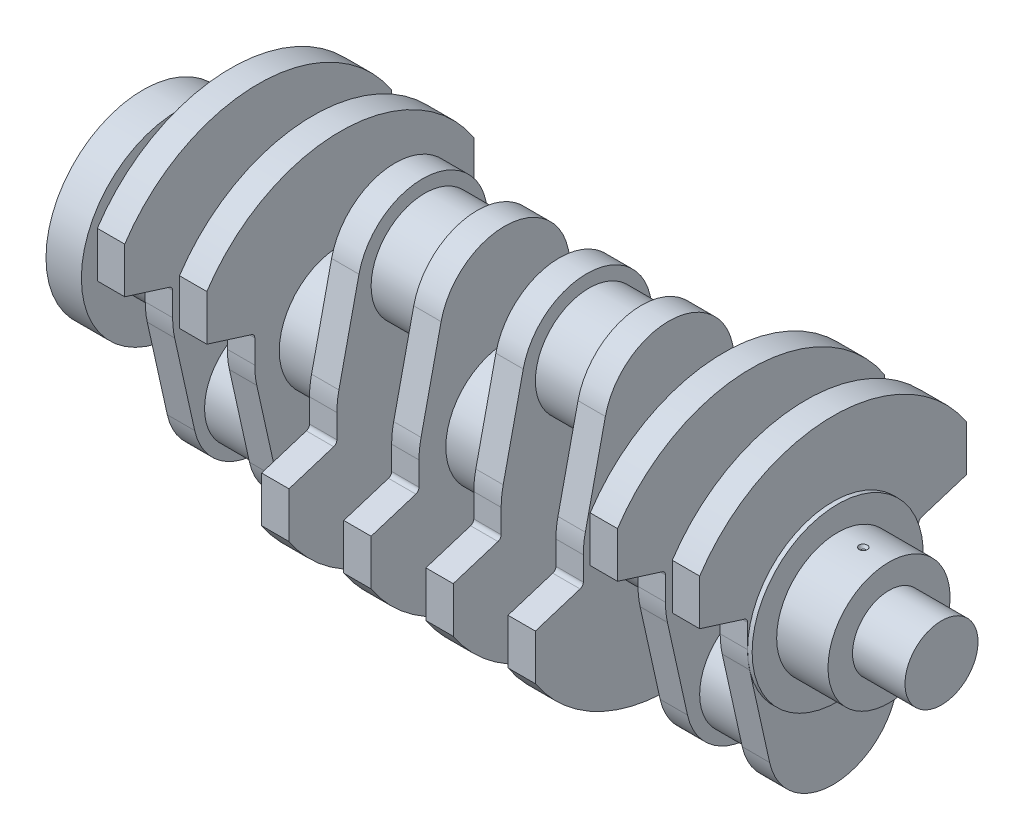
SolidWorks part; units mm, degrees
ref_plane "Plano frontal" through (0, 0, 0) normal (0, 0, 1) x (1, 0, 0)
ref_plane "Plano superior" through (0, 0, 0) normal (0, 1, 0) x (1, 0, 0)
ref_plane "Plano direito" through (0, 0, 0) normal (1, 0, 0) x (0, 0, -1)
sketch "Esboço1" plane through (0, 0, 0) normal (1, 0, 0) x (0, 0, -1)
  circle A0 centre (0, 0) radius 16
  dimension "D1" = 32
extrude "Extrusão1" add sketch "Esboço1" against normal blind 23
sketch "Esboço2" plane through (-23, 0, 0) normal (-1, 0, 0) x (0, 0, 1)
  circle A0 centre (0, 0) radius 26.75
  dimension "D1" = 53.5
extrude "Extrusão2" add sketch "Esboço2" along normal blind 22.5
ref_plane "Plano1" through (-47.5, 0, 0) normal (-1, 0, 0) x (0, 0, 1)
sketch "Esboço5" plane through (-47.5, 0, 0) normal (-1, 0, 0) x (0, 0, 1)
  line L1 (-36.6075, -8.1325) -> (-27.8217, -47.6807)
  line L2 (36.6075, -8.1325) -> (27.8217, -47.6807)
  line L3 (0, 67.381) -> (0, 70) construction
  line L5 (-58.5, 38.4415) -> (-58.5, 18.4415)
  line L6 (58.5, 38.4415) -> (58.5, 18.4415)
  line L7 (-58.5, 18.4415) -> (-37.5, 11.8215)
  line L8 (58.5, 18.4415) -> (37.5, 11.8215)
  line L9 (-37.5, 11.8215) -> (-37.5, 0)
  line L10 (37.5, 11.8215) -> (37.5, 0)
  arc A0 (36.6075, -8.1325) -> (37.5, 0) centre (0, 0) ccw
  arc A1 (-27.8217, -47.6807) -> (27.8217, -47.6807) centre (0, -41.5) ccw
  arc A2 (-58.5, 38.4415) -> (58.5, 38.4415) centre (0, 0) cw
  arc A3 (-37.5, 0) -> (-36.6075, -8.1325) centre (0, 0) ccw
  dimension "D1" = 75
  dimension "D3" = 57
  dimension "D4" = 70
  dimension "D2" = 41.5
  dimension "D5" = 20
  dimension "D6" = 20
extrude "Extrusão4" add sketch "Esboço5" along normal blind 12 separate body
fillet "Filete1" radius 2 1 edges at (-53.5, 11.8215, -37.5)
fillet "Filete2" radius 2 1 edges at (-53.5, 11.8215, 37.5)
ref_plane "Plano2" through (-83.5, 0, 0) normal (-1, 0, 0) x (0, 0, 1)
sketch "Esboço9" plane through (-83.5, 0, 0) normal (-1, 0, 0) x (0, 0, 1)
  line L24 (27.8217, -47.6807) -> (36.6075, -8.1325)
  line L25 (37.5, 0) -> (37.5, 10.3549)
  line L26 (38.8987, 12.2624) -> (58.5, 18.4415)
  line L27 (58.5, 18.4415) -> (58.5, 38.4415)
  line L28 (-58.5, 38.4415) -> (-58.5, 18.4415)
  line L29 (-58.5, 18.4415) -> (-38.8987, 12.2624)
  line L30 (-37.5, 10.3549) -> (-37.5, 0)
  line L31 (-36.6075, -8.1325) -> (-27.8217, -47.6807)
  line L32 (27.8217, -47.6807) -> (36.6075, -8.1325)
  line L33 (37.5, 0) -> (37.5, 10.3549)
  line L34 (38.8987, 12.2624) -> (58.5, 18.4415)
  line L35 (58.5, 18.4415) -> (58.5, 38.4415)
  line L36 (-58.5, 38.4415) -> (-58.5, 18.4415)
  line L37 (-58.5, 18.4415) -> (-38.8987, 12.2624)
  line L38 (-37.5, 10.3549) -> (-37.5, 0)
  line L39 (-36.6075, -8.1325) -> (-27.8217, -47.6807)
  arc A18 (-27.8217, -47.6807) -> (27.8217, -47.6807) centre (0, -41.5) ccw
  arc A19 (36.6075, -8.1325) -> (37.5, 0) centre (0, 0) ccw
  arc A20 (38.8987, 12.2624) -> (37.5, 10.3549) centre (39.5, 10.3549) ccw
  arc A21 (58.5, 38.4415) -> (-58.5, 38.4415) centre (0, 0) ccw
  arc A22 (-37.5, 10.3549) -> (-38.8987, 12.2624) centre (-39.5, 10.3549) ccw
  arc A23 (-37.5, 0) -> (-36.6075, -8.1325) centre (0, 0) ccw
  arc A24 (-27.8217, -47.6807) -> (27.8217, -47.6807) centre (0, -41.5) ccw
  arc A25 (36.6075, -8.1325) -> (37.5, 0) centre (0, 0) ccw
  arc A26 (38.8987, 12.2624) -> (37.5, 10.3549) centre (39.5, 10.3549) ccw
  arc A27 (58.5, 38.4415) -> (-58.5, 38.4415) centre (0, 0) ccw
  arc A28 (-37.5, 10.3549) -> (-38.8987, 12.2624) centre (-39.5, 10.3549) ccw
  arc A29 (-37.5, 0) -> (-36.6075, -8.1325) centre (0, 0) ccw
  dimension "D1" = 0
sketch "Esboço10" plane through (-59.5, 0, 0) normal (-1, 0, 0) x (0, 0, 1)
  circle A0 centre (0, -41.5) radius 23.5
  dimension "D1" = 47
extrude "Extrusão7" add sketch "Esboço10" along normal blind 23
extrude "Extrusão8" add sketch "Esboço9" along normal blind 12
ref_plane "Plano5" through (-119.5, 0, 0) normal (-1, 0, 0) x (0, 0, 1)
sketch "Esboço16" plane through (-119.5, 0, 0) normal (-1, 0, 0) x (0, 0, 1)
  line L17 (37.5, 0) -> (37.5, -10.3549)
  line L18 (38.8987, -12.2624) -> (58.5, -18.4415)
  line L19 (-58.5, -38.4415) -> (-58.5, -18.4415)
  line L20 (-58.5, -18.4415) -> (-38.8987, -12.2624)
  line L21 (-37.5, -10.3549) -> (-37.5, 0)
  line L22 (58.5, -18.4415) -> (58.5, -38.4415)
  line L23 (27.8217, 47.6807) -> (36.6075, 8.1325)
  line L24 (-36.6075, 8.1325) -> (-27.8217, 47.6807)
  arc A12 (-37.5, -10.3549) -> (-38.8987, -12.2624) centre (-39.5, -10.3549) cw
  arc A13 (38.8987, -12.2624) -> (37.5, -10.3549) centre (39.5, -10.3549) cw
  arc A14 (-37.5, 0) -> (-36.6075, 8.1325) centre (0, 0) cw
  arc A15 (36.6075, 8.1325) -> (37.5, 0) centre (0, 0) cw
  arc A16 (58.5, -38.4415) -> (-58.5, -38.4415) centre (0, 0) cw
  arc A17 (-27.8217, 47.6807) -> (27.8217, 47.6807) centre (0, 41.5) cw
extrude "Extrusão14" add sketch "Esboço16" along normal blind 12 separate body
ref_plane "Plano6" through (-155.5, 0, 0) normal (-1, 0, 0) x (0, 0, 1)
sketch "Esboço17" plane through (-155.5, 0, 0) normal (-1, 0, 0) x (0, 0, 1)
  line L16 (-38.8987, -12.2624) -> (-58.5, -18.4415)
  line L17 (-58.5, -18.4415) -> (-58.5, -38.4415)
  line L18 (58.5, -38.4415) -> (58.5, -18.4415)
  line L19 (58.5, -18.4415) -> (38.8987, -12.2624)
  line L20 (37.5, -10.3549) -> (37.5, 0)
  line L21 (36.6075, 8.1325) -> (27.8217, 47.6807)
  line L22 (-27.8217, 47.6807) -> (-36.6075, 8.1325)
  line L23 (-37.5, 0) -> (-37.5, -10.3549)
  line L24 (-38.8987, -12.2624) -> (-58.5, -18.4415)
  line L25 (-58.5, -18.4415) -> (-58.5, -38.4415)
  line L26 (58.5, -38.4415) -> (58.5, -18.4415)
  line L27 (58.5, -18.4415) -> (38.8987, -12.2624)
  line L28 (37.5, -10.3549) -> (37.5, 0)
  line L29 (36.6075, 8.1325) -> (27.8217, 47.6807)
  line L30 (-27.8217, 47.6807) -> (-36.6075, 8.1325)
  line L31 (-37.5, 0) -> (-37.5, -10.3549)
  arc A12 (-38.8987, -12.2624) -> (-37.5, -10.3549) centre (-39.5, -10.3549) ccw
  arc A13 (-58.5, -38.4415) -> (58.5, -38.4415) centre (0, 0) ccw
  arc A14 (37.5, -10.3549) -> (38.8987, -12.2624) centre (39.5, -10.3549) ccw
  arc A15 (37.5, 0) -> (36.6075, 8.1325) centre (0, 0) ccw
  arc A16 (27.8217, 47.6807) -> (-27.8217, 47.6807) centre (0, 41.5) ccw
  arc A17 (-36.6075, 8.1325) -> (-37.5, 0) centre (0, 0) ccw
  arc A18 (-38.8987, -12.2624) -> (-37.5, -10.3549) centre (-39.5, -10.3549) ccw
  arc A19 (-58.5, -38.4415) -> (58.5, -38.4415) centre (0, 0) ccw
  arc A20 (37.5, -10.3549) -> (38.8987, -12.2624) centre (39.5, -10.3549) ccw
  arc A21 (37.5, 0) -> (36.6075, 8.1325) centre (0, 0) ccw
  arc A22 (27.8217, 47.6807) -> (-27.8217, 47.6807) centre (0, 41.5) ccw
  arc A23 (-36.6075, 8.1325) -> (-37.5, 0) centre (0, 0) ccw
  dimension "D1" = 0
extrude "Extrusão15" add sketch "Esboço17" along normal blind 12 separate body
ref_plane "Plano7" through (-191.5, 0, 0) normal (-1, 0, 0) x (0, 0, 1)
sketch "Esboço18" plane through (-191.5, 0, 0) normal (-1, 0, 0) x (0, 0, 1)
  line L16 (-38.8987, -12.2624) -> (-58.5, -18.4415)
  line L17 (-58.5, -18.4415) -> (-58.5, -38.4415)
  line L18 (58.5, -38.4415) -> (58.5, -18.4415)
  line L19 (58.5, -18.4415) -> (38.8987, -12.2624)
  line L20 (37.5, -10.3549) -> (37.5, 0)
  line L21 (36.6075, 8.1325) -> (27.8217, 47.6807)
  line L22 (-27.8217, 47.6807) -> (-36.6075, 8.1325)
  line L23 (-37.5, 0) -> (-37.5, -10.3549)
  line L24 (-38.8987, -12.2624) -> (-58.5, -18.4415)
  line L25 (-58.5, -18.4415) -> (-58.5, -38.4415)
  line L26 (58.5, -38.4415) -> (58.5, -18.4415)
  line L27 (58.5, -18.4415) -> (38.8987, -12.2624)
  line L28 (37.5, -10.3549) -> (37.5, 0)
  line L29 (36.6075, 8.1325) -> (27.8217, 47.6807)
  line L30 (-27.8217, 47.6807) -> (-36.6075, 8.1325)
  line L31 (-37.5, 0) -> (-37.5, -10.3549)
  arc A12 (-38.8987, -12.2624) -> (-37.5, -10.3549) centre (-39.5, -10.3549) ccw
  arc A13 (-58.5, -38.4415) -> (58.5, -38.4415) centre (0, 0) ccw
  arc A14 (37.5, -10.3549) -> (38.8987, -12.2624) centre (39.5, -10.3549) ccw
  arc A15 (37.5, 0) -> (36.6075, 8.1325) centre (0, 0) ccw
  arc A16 (27.8217, 47.6807) -> (-27.8217, 47.6807) centre (0, 41.5) ccw
  arc A17 (-36.6075, 8.1325) -> (-37.5, 0) centre (0, 0) ccw
  arc A18 (-38.8987, -12.2624) -> (-37.5, -10.3549) centre (-39.5, -10.3549) ccw
  arc A19 (-58.5, -38.4415) -> (58.5, -38.4415) centre (0, 0) ccw
  arc A20 (37.5, -10.3549) -> (38.8987, -12.2624) centre (39.5, -10.3549) ccw
  arc A21 (37.5, 0) -> (36.6075, 8.1325) centre (0, 0) ccw
  arc A22 (27.8217, 47.6807) -> (-27.8217, 47.6807) centre (0, 41.5) ccw
  arc A23 (-36.6075, 8.1325) -> (-37.5, 0) centre (0, 0) ccw
  dimension "D1" = 0
extrude "Extrusão16" add sketch "Esboço18" along normal blind 12 separate body
ref_plane "Plano8" through (-227.5, 0, 0) normal (-1, 0, 0) x (0, 0, 1)
sketch "Esboço19" plane through (-227.5, 0, 0) normal (-1, 0, 0) x (0, 0, 1)
  line L16 (-38.8987, -12.2624) -> (-58.5, -18.4415)
  line L17 (-58.5, -18.4415) -> (-58.5, -38.4415)
  line L18 (58.5, -38.4415) -> (58.5, -18.4415)
  line L19 (58.5, -18.4415) -> (38.8987, -12.2624)
  line L20 (37.5, -10.3549) -> (37.5, 0)
  line L21 (36.6075, 8.1325) -> (27.8217, 47.6807)
  line L22 (-27.8217, 47.6807) -> (-36.6075, 8.1325)
  line L23 (-37.5, 0) -> (-37.5, -10.3549)
  line L24 (-38.8987, -12.2624) -> (-58.5, -18.4415)
  line L25 (-58.5, -18.4415) -> (-58.5, -38.4415)
  line L26 (58.5, -38.4415) -> (58.5, -18.4415)
  line L27 (58.5, -18.4415) -> (38.8987, -12.2624)
  line L28 (37.5, -10.3549) -> (37.5, 0)
  line L29 (36.6075, 8.1325) -> (27.8217, 47.6807)
  line L30 (-27.8217, 47.6807) -> (-36.6075, 8.1325)
  line L31 (-37.5, 0) -> (-37.5, -10.3549)
  arc A12 (-38.8987, -12.2624) -> (-37.5, -10.3549) centre (-39.5, -10.3549) ccw
  arc A13 (-58.5, -38.4415) -> (58.5, -38.4415) centre (0, 0) ccw
  arc A14 (37.5, -10.3549) -> (38.8987, -12.2624) centre (39.5, -10.3549) ccw
  arc A15 (37.5, 0) -> (36.6075, 8.1325) centre (0, 0) ccw
  arc A16 (27.8217, 47.6807) -> (-27.8217, 47.6807) centre (0, 41.5) ccw
  arc A17 (-36.6075, 8.1325) -> (-37.5, 0) centre (0, 0) ccw
  arc A18 (-38.8987, -12.2624) -> (-37.5, -10.3549) centre (-39.5, -10.3549) ccw
  arc A19 (-58.5, -38.4415) -> (58.5, -38.4415) centre (0, 0) ccw
  arc A20 (37.5, -10.3549) -> (38.8987, -12.2624) centre (39.5, -10.3549) ccw
  arc A21 (37.5, 0) -> (36.6075, 8.1325) centre (0, 0) ccw
  arc A22 (27.8217, 47.6807) -> (-27.8217, 47.6807) centre (0, 41.5) ccw
  arc A23 (-36.6075, 8.1325) -> (-37.5, 0) centre (0, 0) ccw
  dimension "D1" = 0
extrude "Extrusão17" add sketch "Esboço19" along normal blind 12 separate body
sketch "Esboço20" plane through (-95.5, 0, 0) normal (-1, 0, 0) x (0, 0, 1)
  circle A0 centre (0, 0) radius 26.75
  dimension "D1" = 53.5
extrude "Extrusão18" add sketch "Esboço20" along normal blind 23
sketch "Esboço21" plane through (-131.5, 0, 0) normal (-1, 0, 0) x (0, 0, 1)
  circle A0 centre (0, 41.5) radius 23.5
  dimension "D1" = 47
extrude "Extrusão19" add sketch "Esboço21" along normal blind 23
sketch "Esboço22" plane through (-167.5, 0, 0) normal (-1, 0, 0) x (0, 0, 1)
  circle A0 centre (0, 0) radius 26.75
  dimension "D1" = 53.5
extrude "Extrusão21" add sketch "Esboço22" along normal blind 23
sketch "Esboço23" plane through (-203.5, 0, 0) normal (-1, 0, 0) x (0, 0, 1)
  circle A0 centre (0, 41.5) radius 23.5
  dimension "D1" = 47
extrude "Extrusão22" add sketch "Esboço23" along normal blind 23
ref_plane "Plano9" through (-263.5, 0, 0) normal (-1, 0, 0) x (0, 0, 1)
sketch "Esboço25" plane through (-263.5, 0, 0) normal (-1, 0, 0) x (0, 0, 1)
  line L1 (58.5, 38.4415) -> (58.5, 18.4415)
  line L2 (58.5, 18.4415) -> (38.8987, 12.2624)
  line L3 (37.5, 10.3549) -> (37.5, 0)
  line L4 (36.6075, -8.1325) -> (27.8217, -47.6807)
  line L5 (-27.8217, -47.6807) -> (-36.6075, -8.1325)
  line L6 (-37.5, 0) -> (-37.5, 10.3549)
  line L7 (-38.8987, 12.2624) -> (-58.5, 18.4415)
  line L24 (-58.5, 18.4415) -> (-58.5, 38.4415)
  arc A0 (37.5, 10.3549) -> (38.8987, 12.2624) centre (39.5, 10.3549) cw
  arc A1 (37.5, 0) -> (36.6075, -8.1325) centre (0, 0) cw
  arc A2 (27.8217, -47.6807) -> (-27.8217, -47.6807) centre (0, -41.5) cw
  arc A3 (-36.6075, -8.1325) -> (-37.5, 0) centre (0, 0) cw
  arc A4 (-38.8987, 12.2624) -> (-37.5, 10.3549) centre (-39.5, 10.3549) cw
  arc A5 (-58.5, 38.4415) -> (58.5, 38.4415) centre (0, 0) cw
extrude "Extrusão23" add sketch "Esboço25" along normal blind 12 separate body
ref_plane "Plano10" through (-299.5, 0, 0) normal (-1, 0, 0) x (0, 0, 1)
sketch "Esboço26" plane through (-299.5, 0, 0) normal (-1, 0, 0) x (0, 0, 1)
  line L16 (-58.5, 38.4415) -> (-58.5, 18.4415)
  line L17 (-58.5, 18.4415) -> (-38.8987, 12.2624)
  line L18 (-37.5, 10.3549) -> (-37.5, 0)
  line L19 (-36.6075, -8.1325) -> (-27.8217, -47.6807)
  line L20 (27.8217, -47.6807) -> (36.6075, -8.1325)
  line L21 (37.5, 0) -> (37.5, 10.3549)
  line L22 (38.8987, 12.2624) -> (58.5, 18.4415)
  line L23 (58.5, 18.4415) -> (58.5, 38.4415)
  line L24 (-58.5, 38.4415) -> (-58.5, 18.4415)
  line L25 (-58.5, 18.4415) -> (-38.8987, 12.2624)
  line L26 (-37.5, 10.3549) -> (-37.5, 0)
  line L27 (-36.6075, -8.1325) -> (-27.8217, -47.6807)
  line L28 (27.8217, -47.6807) -> (36.6075, -8.1325)
  line L29 (37.5, 0) -> (37.5, 10.3549)
  line L30 (38.8987, 12.2624) -> (58.5, 18.4415)
  line L31 (58.5, 18.4415) -> (58.5, 38.4415)
  arc A12 (58.5, 38.4415) -> (-58.5, 38.4415) centre (0, 0) ccw
  arc A13 (-37.5, 10.3549) -> (-38.8987, 12.2624) centre (-39.5, 10.3549) ccw
  arc A14 (-37.5, 0) -> (-36.6075, -8.1325) centre (0, 0) ccw
  arc A15 (-27.8217, -47.6807) -> (27.8217, -47.6807) centre (0, -41.5) ccw
  arc A16 (36.6075, -8.1325) -> (37.5, 0) centre (0, 0) ccw
  arc A17 (38.8987, 12.2624) -> (37.5, 10.3549) centre (39.5, 10.3549) ccw
  arc A18 (58.5, 38.4415) -> (-58.5, 38.4415) centre (0, 0) ccw
  arc A19 (-37.5, 10.3549) -> (-38.8987, 12.2624) centre (-39.5, 10.3549) ccw
  arc A20 (-37.5, 0) -> (-36.6075, -8.1325) centre (0, 0) ccw
  arc A21 (-27.8217, -47.6807) -> (27.8217, -47.6807) centre (0, -41.5) ccw
  arc A22 (36.6075, -8.1325) -> (37.5, 0) centre (0, 0) ccw
  arc A23 (38.8987, 12.2624) -> (37.5, 10.3549) centre (39.5, 10.3549) ccw
  dimension "D1" = 0
extrude "Extrusão24" add sketch "Esboço26" along normal blind 12 separate body
sketch "Esboço27" plane through (-239.5, 0, 0) normal (-1, 0, 0) x (0, 0, 1)
  circle A0 centre (0, 0) radius 26.75
  dimension "D1" = 53.5
extrude "Extrusão25" add sketch "Esboço27" along normal blind 24
sketch "Esboço28" plane through (-275.5, 0, 0) normal (-1, 0, 0) x (0, 0, 1)
  circle A0 centre (0, -41.5) radius 23.5
  dimension "D1" = 47
extrude "Extrusão26" add sketch "Esboço28" along normal blind 24
sketch "Esboço29" plane through (-311.5, 0, 0) normal (-1, 0, 0) x (0, 0, 1)
  circle A0 centre (0, 0) radius 26.75
  dimension "D1" = 53.5
extrude "Extrusão27" add sketch "Esboço29" along normal blind 23
sketch "Esboço30" plane through (-334.5, 0, 0) normal (-1, 0, 0) x (0, 0, 1)
  circle A0 centre (0, 0) radius 42.5
  dimension "D1" = 85
extrude "Extrusão28" add sketch "Esboço30" along normal blind 15.5
sketch "Esboço31" plane through (-350, 0, 0) normal (-1, 0, 0) x (0, 0, 1)
  circle A0 centre (0, 0) radius 21.5
  dimension "D1" = 43
extrude "Extrusão29" add sketch "Esboço31" along normal blind 5.5
ref_plane "Plano11" through (-362.5, 0, 0) normal (-1, 0, 0) x (0, 0, 1)
sketch "Esboço33" plane through (-362.5, 0, 0) normal (-1, 0, 0) x (0, 0, 1)
  circle A0 centre (0, 0) radius 15
  dimension "D1" = 30
extrude "Extrusão34" add sketch "Esboço33" against normal blind 7 draft 42 draft outward yes
sketch "Esboço34" plane through (-362.5, 0, 0) normal (-1, 0, 0) x (0, 0, 1)
  circle A0 centre (0, 0) radius 8
  dimension "D1" = 16
extrude "Extrusão35" cut sketch "Esboço34" against normal blind 25
sketch "Esboço35" plane through (-350, 0, 0) normal (-1, 0, 0) x (0, 0, 1)
  circle A0 centre (0, 0) radius 32
  dimension "D1" = 64
sketch "Esboço40" plane through (0, 0, 0) normal (0, 0, 1) x (1, 0, 0)
  line L0 (-34.25, 27.9789) -> (-34.25, 25.3608)
  line L1 (-34.25, 25.3608) -> (-33.25, 25.3608)
  line L2 (-33.25, 25.3608) -> (-31.75, 27.9789)
  line L3 (-31.75, 27.9789) -> (-34.25, 27.9789)
  dimension "D1" = 1
  dimension "D2" = 2.5
  dimension "D3" = 11.25
revolve "Corte-Revolução3" cut sketch "Esboço40" angle 360 about L0
sketch "Esboço41" plane through (-45.5, 0, 0) normal (-1, 0, 0) x (0, 0, 1)
  circle A0 centre (0, 0) radius 37.5
extrude "Extrusão42" add sketch "Esboço41" along normal blind 2
